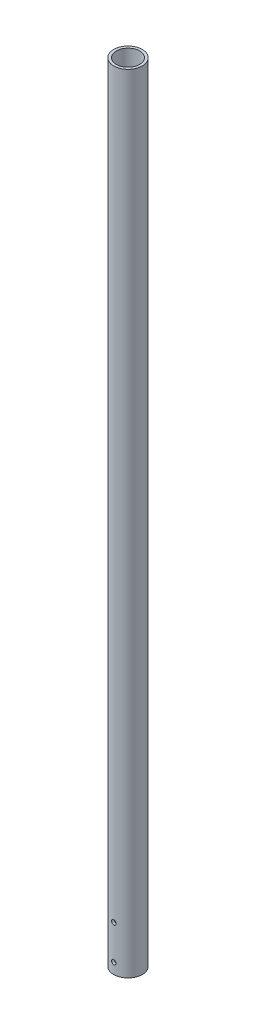
SolidWorks part; units mm, degrees
ref_plane "Front Plane" through (0, 0, 0) normal (0, 0, 1) x (1, 0, 0)
ref_plane "Top Plane" through (0, 0, 0) normal (0, 1, 0) x (1, 0, 0)
ref_plane "Right Plane" through (0, 0, 0) normal (1, 0, 0) x (0, 0, -1)
sketch "Sketch1" plane through (0, 0, 0) normal (0, 1, 0) x (1, 0, 0)
  circle A0 centre (0, 0) radius 21.082
  circle A1 centre (0, 0) radius 17.272
  dimension "D1" = 34.544
  dimension "1.66" = 42.164
extrude "Boss-Extrude1" add sketch "Sketch1" along normal blind 1160.4625
ref_plane "Plane1" through (0, 0, 21.082) normal (0, 0, 1) x (1, 0, 0)
sketch "Sketch2" plane through (0, 0, 21.082) normal (0, 0, 1) x (1, 0, 0)
  line L2 (-21.082, 0) -> (21.082, 0) construction
  point P0 (0, 15.875)
  point P1 (0, 66.675)
  dimension "D2" = 50.8
  dimension "D3" = 15.875
hole_wizard "1/4 Clearance Hole1" positions "Sketch3" profile "Sketch4" hole size "1/4" standard "ANSI Inch" end condition through all
sketch "Sketch3" plane through (0, 0, 21.082) normal (0, 0, 1) x (1, 0, 0)
  point P0 (0, 15.875)
  point P3 (0, 66.675)
sketch "Sketch4" plane through (0, 15.875, 21.082) normal (1, 0, 0) x (0, -1, 0)
  line L0 (0, 0) -> (0, 42.164)
  line L1 (0, 42.164) -> (3.3782, 42.164)
  line L2 (3.3782, 42.164) -> (3.3782, 0)
  line L5 (3.3782, 0) -> (0, 0)
  line L11 (0, -6.35) -> (0, 107.95) construction
  dimension "Thru Hole Dia." = 6.7564
  dimension "Thru Hole Depth" = 42.164
